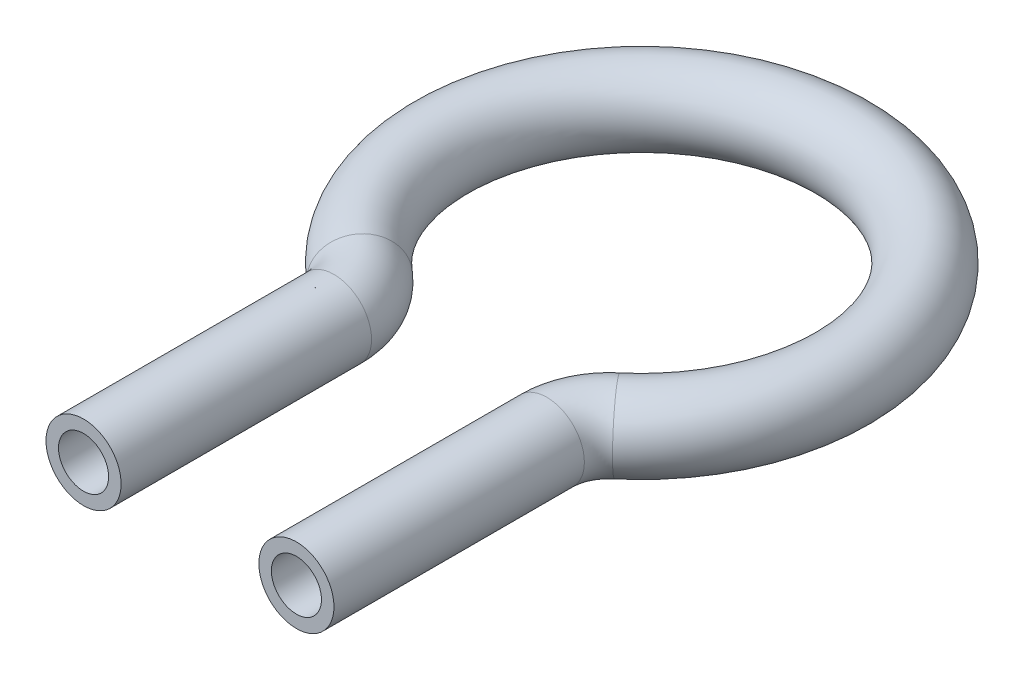
SolidWorks part; units mm, degrees
ref_plane "Front Plane" through (0, 0, 0) normal (0, 0, 1) x (1, 0, 0)
ref_plane "Top Plane" through (0, 0, 0) normal (0, 1, 0) x (1, 0, 0)
ref_plane "Right Plane" through (0, 0, 0) normal (1, 0, 0) x (0, 0, -1)
sketch "Sketch1" plane through (0, 0, 0) normal (0, 1, 0) x (1, 0, 0)
  line L1 (8.5, -16.0857) -> (8.5, -36.0857)
  line L2 (-8.5, -16.0857) -> (-8.5, -36.0857)
  arc A0 (-10.2857, -12.2558) -> (10.2857, -12.2558) centre (0, 0) cw
  arc A1 (10.2857, -12.2558) -> (8.5, -16.0857) centre (13.5, -16.0857) ccw
  arc A2 (-10.2857, -12.2558) -> (-8.5, -16.0857) centre (-13.5, -16.0857) cw
  point P10 (0, 0)
  point P12 (-8.5, -34.0712)
  point P13 (0, 0)
  dimension "D1" = 16
  dimension "D3" = 5
  dimension "D4" = 5
  dimension "D2" = 20
  dimension "D5" = 17
ref_plane "Plane1" through (-8.5, 0, 36.0857) normal (0, 0, -1) x (-1, 0, 0)
sketch "Sketch2" plane through (-8.5, 0, 36.0857) normal (0, 0, -1) x (-1, 0, 0)
  circle A0 centre (0, 0) radius 3
  circle A1 centre (0, 0) radius 2
  point P4 (0, 0)
  point P5 (0, 0)
  dimension "D1" = 6
  dimension "D2" = 4
sweep "Sweep1" add profiles "Sketch2" path "Sketch1"
